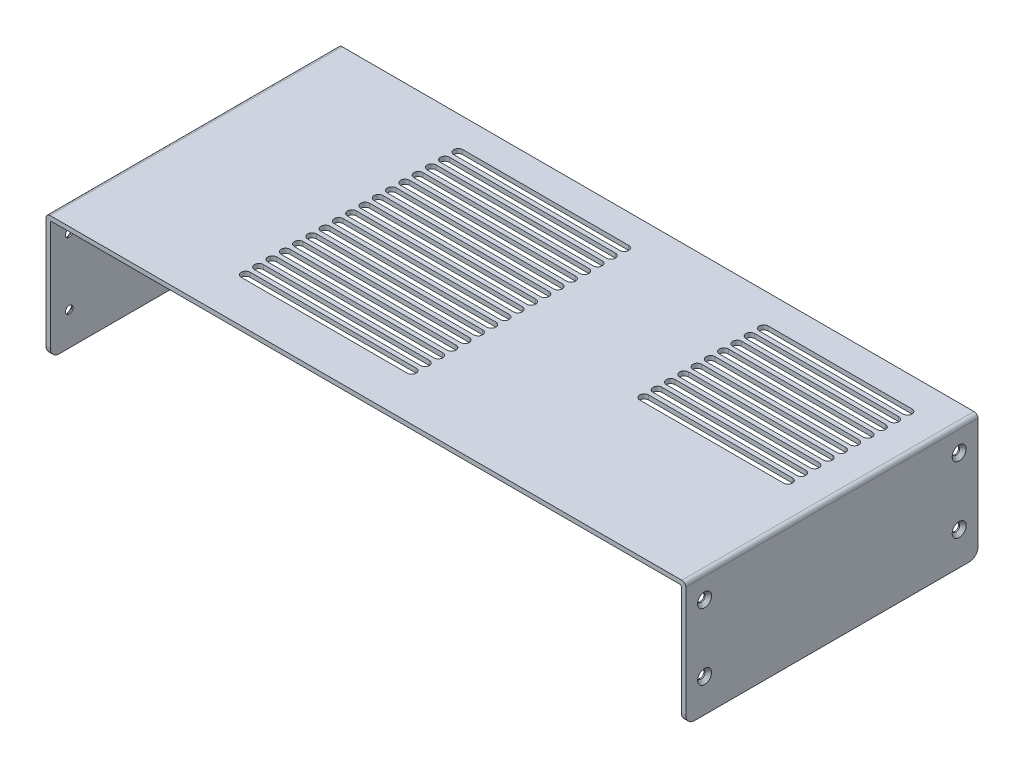
SolidWorks part; units mm, degrees
ref_plane "Front Plane" through (0, 0, 0) normal (0, 0, 1) x (1, 0, 0)
ref_plane "Top Plane" through (0, 0, 0) normal (0, 1, 0) x (1, 0, 0)
ref_plane "Right Plane" through (0, 0, 0) normal (1, 0, 0) x (0, 0, -1)
sketch "Sketch1" plane through (0, 0, 0) normal (0, 0, 1) x (1, 0, 0)
  line L0 (0, 0) -> (-2, 0)
  line L1 (-2, 0) -> (-2, 54.2)
  line L2 (-0.2, 56) -> (285.2, 56)
  line L3 (287, 54.2) -> (287, 0)
  line L4 (287, 0) -> (285, 0)
  line L5 (285, 0) -> (285, 53.5)
  line L6 (284.5, 54) -> (0.5, 54)
  line L7 (0, 53.5) -> (0, 0)
  arc A0 (285, 53.5) -> (284.5, 54) centre (284.5, 53.5) ccw
  arc A1 (0.5, 54) -> (0, 53.5) centre (0.5, 53.5) ccw
  arc A2 (-2, 54.2) -> (-0.2, 56) centre (-0.2, 54.2) cw
  arc A3 (285.2, 56) -> (287, 54.2) centre (285.2, 54.2) cw
  point P13 (0, 54)
  dimension "D5" = 0.5
  dimension "D6" = 1.8
  dimension "D1" = 54
  dimension "D2" = 285
  dimension "D3" = 2
  dimension "D4" = 2
extrude "Boss-Extrude1" add sketch "Sketch1" along normal blind 132
hole_wizard "CSK for M3 Flat Head Machine Screw1" positions "Sketch3" profile "Sketch2" countersink size "M3" standard "Ansi Metric"
sketch "Sketch3" plane through (-2, 0, 0) normal (-1, 0, 0) x (0, 0, 1)
  point P0 (8.5, 45)
  point P1 (8.5, 15)
  point P3 (123.5, 45)
  point P5 (123.5, 15)
sketch "Sketch2" plane through (-2, 45, 8.5) normal (0, 1, 0) x (0, 0, 1)
  line L0 (0, 0) -> (0, 6.0215)
  line L1 (0, 6.0215) -> (1.7, 5)
  line L2 (1.7, 5) -> (1.7, 1.45)
  line L3 (1.7, 1.45) -> (3.15, 0)
  line L5 (3.15, 0) -> (0, 0)
  line L6 (-1.7, 1.45) -> (-3.15, 0) construction
  line L10 (0, 6.0215) -> (-1.7, 5) construction
  line L11 (0, -6.35) -> (0, 107.95) construction
  dimension "Hole Dia." = 3.4
  dimension "Hole Depth" = 5
  dimension "Near C'Sink Dia." = 6.3
  dimension "Near C'Sink Angle" = 90
  dimension "Drill Angle" = 118
hole_wizard "CSK for M3 Flat Head Machine Screw2" positions "Sketch5" profile "Sketch4" countersink size "M3" standard "Ansi Metric"
sketch "Sketch5" plane through (287, 0, 0) normal (1, 0, 0) x (0, 0, -1)
  point P0 (-123.5, 45)
  point P1 (-123.5, 15)
  point P3 (-8.5, 45)
  point P5 (-8.5, 15)
sketch "Sketch4" plane through (287, 45, 123.5) normal (0, 1, 0) x (0, 0, -1)
  line L0 (0, 0) -> (0, 6.0215)
  line L1 (0, 6.0215) -> (1.7, 5)
  line L2 (1.7, 5) -> (1.7, 1.45)
  line L3 (1.7, 1.45) -> (3.15, 0)
  line L5 (3.15, 0) -> (0, 0)
  line L6 (-1.7, 1.45) -> (-3.15, 0) construction
  line L10 (0, 6.0215) -> (-1.7, 5) construction
  line L11 (0, -6.35) -> (0, 107.95) construction
  dimension "Hole Dia." = 3.4
  dimension "Hole Depth" = 5
  dimension "Near C'Sink Dia." = 6.3
  dimension "Near C'Sink Angle" = 90
  dimension "Drill Angle" = 118
sketch "Sketch6" plane through (0, 56, 0) normal (0, 1, 0) x (1, 0, 0)
  line L0 (67.2, -15) -> (142.2, -15) construction
  line L1 (67.2, -13) -> (142.2, -13)
  line L2 (67.2, -17) -> (142.2, -17)
  line L3 (285.2, 0) -> (-0.2, 0) construction
  line L6 (285.2, -132) -> (285.2, 0) construction
  arc A0 (67.2, -13) -> (67.2, -17) centre (67.2, -15) ccw
  arc A1 (142.2, -17) -> (142.2, -13) centre (142.2, -15) ccw
  point P2 (104.7, -15)
  dimension "D3" = 2
  dimension "D1" = 15
  dimension "D2" = 143
  dimension "D4" = 75
extrude "Cut-Extrude1" cut sketch "Sketch6" against normal blind 5
pattern_linear "LPattern1" count 17 spacing 6 along (0, 0, 1) of "Cut-Extrude1"
sketch "Sketch7" plane through (0, 56, 0) normal (0, 1, 0) x (1, 0, 0)
  line L0 (205.2, -15) -> (270.2, -15) construction
  line L1 (205.2, -13) -> (270.2, -13)
  line L2 (205.2, -17) -> (270.2, -17)
  line L3 (285.2, -132) -> (285.2, 0) construction
  line L4 (285.2, 0) -> (-0.2, 0) construction
  arc A0 (205.2, -13) -> (205.2, -17) centre (205.2, -15) ccw
  arc A1 (270.2, -17) -> (270.2, -13) centre (270.2, -15) ccw
  point P2 (237.7, -15)
  dimension "D3" = 2
  dimension "D1" = 15
  dimension "D2" = 65
  dimension "D4" = 15
extrude "Cut-Extrude2" cut sketch "Sketch7" against normal blind 200
pattern_linear "LPattern2" count 10 spacing 6 along (0, 0, 1) of "Cut-Extrude2"
fillet "Fillet1" radius 4 4 edges at (286, 0, 132) (286, 0, 0) (-1, 0, 132) (-1, 0, 0)
